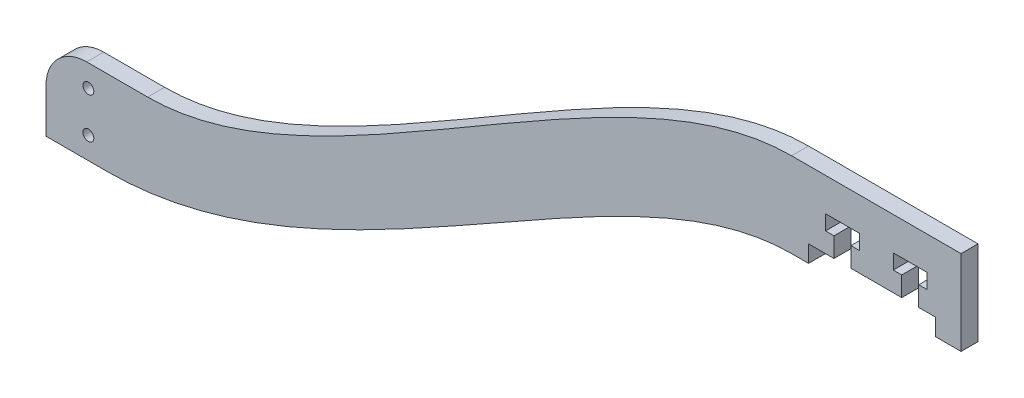
SolidWorks part; units mm, degrees
ref_plane "Front Plane" through (0, 0, 0) normal (0, 0, 1) x (1, 0, 0)
ref_plane "Top Plane" through (0, 0, 0) normal (0, 1, 0) x (1, 0, 0)
ref_plane "Right Plane" through (0, 0, 0) normal (1, 0, 0) x (0, 0, -1)
sketch "Sketch1" plane through (0, 0, 0) normal (0, 0, 1) x (1, 0, 0)
  line L0 (0, 0) -> (3.175, 0)
  line L1 (-139.7, -42.545) -> (-139.7, -50.8)
  line L2 (-71.502, -34.925) -> (-125.3505, -34.925) construction
  line L3 (3.175, 0) -> (3.175, 3.175)
  line L4 (3.175, 3.175) -> (7.9375, 3.175)
  line L5 (31.75, 0) -> (31.75, 15.875)
  line L6 (31.75, 15.875) -> (0, 15.875)
  line L7 (0, -1000) -> (0, 49000) construction
  line L8 (9.525, -988.6477) -> (9.525, 49011.3523) construction
  line L9 (22.225, -989.9681) -> (22.225, 49010.0319) construction
  line L10 (7.9375, 3.175) -> (7.9375, 6.858)
  line L11 (7.9375, 6.858) -> (6.35, 6.858)
  line L12 (6.35, 6.858) -> (6.35, 9.652)
  line L13 (6.35, 9.652) -> (12.7, 9.652)
  line L14 (12.7, 9.652) -> (12.7, 6.858)
  line L15 (12.7, 6.858) -> (11.1125, 6.858)
  line L16 (11.1125, 6.858) -> (11.1125, 3.175)
  line L17 (11.1125, 3.175) -> (20.6375, 3.175)
  line L18 (20.6375, 3.175) -> (20.6375, 6.858)
  line L19 (20.6375, 6.858) -> (19.05, 6.858)
  line L20 (19.05, 6.858) -> (19.05, 9.652)
  line L21 (19.05, 9.652) -> (25.4, 9.652)
  line L22 (25.4, 9.652) -> (25.4, 6.858)
  line L23 (25.4, 6.858) -> (23.8125, 6.858)
  line L24 (23.8125, 6.858) -> (23.8125, 3.175)
  line L25 (23.8125, 3.175) -> (26.9875, 3.175)
  line L26 (-131.7625, -1027.5945) -> (-131.7625, 48972.4055) construction
  line L27 (-128.27, -50.8) -> (-139.7, -50.8)
  line L28 (-120.65, -34.925) -> (-132.08, -34.925)
  line L29 (-127, -288.925) -> (-120.65, -34.925) construction
  line L30 (-71.502, -50.8) -> (-125.3505, -50.8) construction
  line L31 (26.9875, 3.175) -> (26.9875, 0)
  line L32 (26.7231, 15.875) -> (-26.7231, 15.875) construction
  line L33 (26.3977, 0) -> (-26.3989, 0) construction
  line L34 (26.9875, 0) -> (31.75, 0)
  circle A0 centre (-131.7625, -39.0525) radius 1.016
  circle A1 centre (-131.7625, -46.6725) radius 1.016
  arc A2 (-132.08, -34.925) -> (-139.7, -42.545) centre (-132.08, -42.545) ccw
  spline S0 degree 3 poles (-120.65, -34.925) (-86.9947, -34.925) (-33.4039, 15.875) (0, 15.875) knots 0 0 0 0 1 1 1 1
  spline S1 degree 3 poles (-128.27, -50.8) (-84.7243, -50.8) (-32.9979, 0) (0, 0) knots 0 0 0 0 1 1 1 1
  point P23 (9.525, 9.652)
  point P31 (22.225, 9.652)
  point P48 (-139.7, -34.925)
  dimension "D14" = 2.032
  dimension "D17" = 7.62
  dimension "D2" = 15.875
  dimension "D3" = 15.875
  dimension "D4" = 139.7
  dimension "D5" = 31.75
  dimension "D6" = 9.525
  dimension "D7" = 12.7
  dimension "D8" = 6.35
  dimension "D9" = 2.794
  dimension "D10" = 6.477
  dimension "D11" = 3.175
  dimension "D12" = 50.8
  dimension "D13" = 7.9375
  dimension "D15" = 4.1275
  dimension "D16" = 7.62
  dimension "D18" = 3.175
  dimension "D19" = 3.175
  dimension "D20" = 4.7625
extrude "Boss-Extrude1" add sketch "Sketch1" along normal blind 3.175
